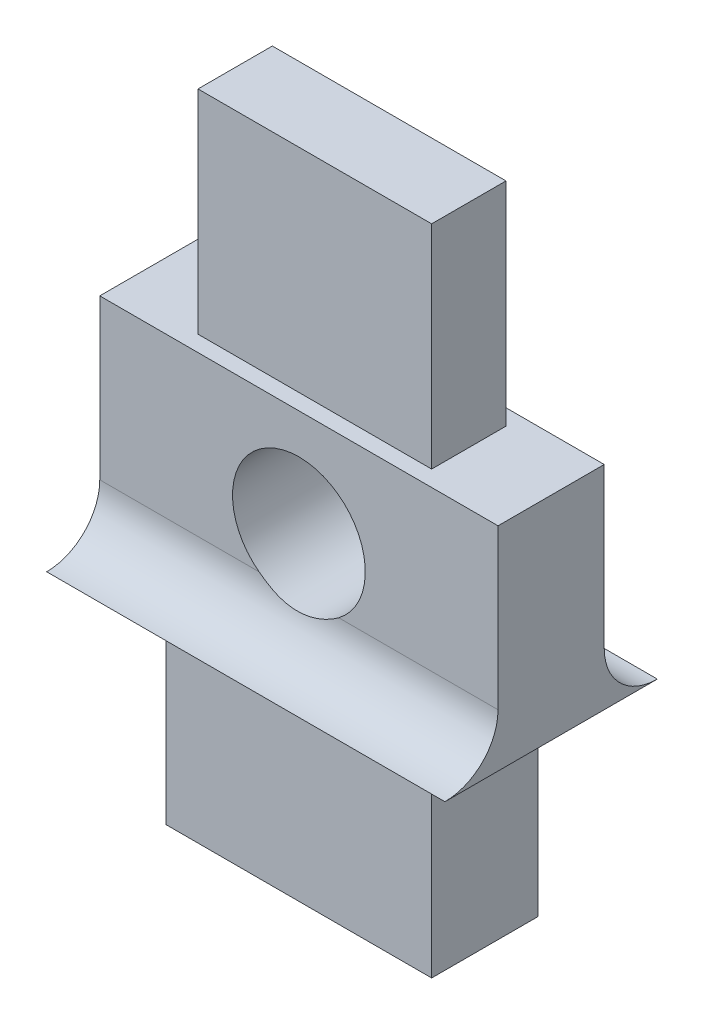
SolidWorks part; units mm, degrees
ref_plane "Front Plane" through (0, 0, 0) normal (0, 0, 1) x (1, 0, 0)
ref_plane "Top Plane" through (0, 0, 0) normal (0, 1, 0) x (1, 0, 0)
ref_plane "Right Plane" through (0, 0, 0) normal (1, 0, 0) x (0, 0, -1)
sketch "Sketch1" plane through (0, 0, 0) normal (0, 0, 1) x (1, 0, 0)
  line L0 (1952.1768, 1466.8841) -> (1957.1768, 1466.8841)
  line L1 (1952.1768, 1454.8841) -> (1957.1768, 1454.8841)
  line L3 (1957.1768, 1458.8841) -> (1957.1768, 1454.8841)
  line L4 (1957.1768, 1458.8841) -> (1958.4268, 1458.8841)
  line L5 (1958.4268, 1462.8841) -> (1958.4268, 1458.8841)
  line L6 (1957.1768, 1462.8841) -> (1957.1768, 1466.8841)
  line L7 (1957.1768, 1462.8841) -> (1958.4268, 1462.8841)
  line L37 (1952.1768, 1458.8841) -> (1950.9268, 1458.8841)
  line L40 (1952.1768, 1458.8841) -> (1952.1768, 1454.8841)
  line L127 (1952.1768, 1462.8841) -> (1950.9268, 1462.8841)
  line L130 (1952.1768, 1462.8841) -> (1952.1768, 1466.8841)
  line L131 (1950.9268, 1462.8841) -> (1950.9268, 1458.8841)
  circle A82 centre (1954.6768, 1460.8841) radius 1.25
  dimension "D1" = 2.5
  dimension "D2" = 1950.9268
  dimension "D3" = 1954.6768
  dimension "D4" = 1957.1768
  dimension "D5" = 1454.8841
  dimension "D6" = 1458.8841
  dimension "D7" = 1460.8841
extrude "Boss-Extrude1" add sketch "Sketch1" along normal blind 2
sketch "Sketch2" plane through (1950.9268, 0, 0) normal (-1, 0, 0) x (0, 0, 1)
  line L0 (1, 1454.8841) -> (1, 1461.8841) construction
  line L1 (2, 1458.8841) -> (2, 1459.8841)
  line L2 (2, 1458.8841) -> (3, 1458.8841)
  line L3 (0, 1458.8841) -> (-1, 1458.8841)
  line L4 (0, 1458.8841) -> (0, 1459.8841)
  arc A0 (2, 1459.8841) -> (3, 1458.8841) centre (3, 1459.8841) ccw
  arc A1 (0, 1459.8841) -> (-1, 1458.8841) centre (-1, 1459.8841) cw
  dimension "D1" = 1
  dimension "D2" = 1
  dimension "D3" = 4
  dimension "D4" = 1
  dimension "D5" = 4
  dimension "D6" = 2
extrude "Boss-Extrude2" add sketch "Sketch2" against normal up to surface (7.5 mm away) up to face at (1958.4268, 1460.8841, 1)
sketch "Sketch3" plane through (0, 0, 2) normal (0, 0, 1) x (1, 0, 0)
  circle A0 centre (1954.6768, 1460.8841) radius 1.25
  dimension "D1" = 2.5
extrude "Cut-Extrude1" cut sketch "Sketch3" against normal through all both and the other way through all
sketch "Sketch4" plane through (0, 1466.8841, 0) normal (0, 1, 0) x (1, 0, 0)
  line L1 (1952.1768, -2) -> (1957.1768, -2)
  line L2 (1952.1768, -2) -> (1952.1768, 0)
  line L3 (1952.1768, 0) -> (1957.1768, 0)
  line L4 (1957.1768, -2) -> (1957.1768, 0)
  line L5 (1952.4768, -1.7) -> (1956.8768, -1.7)
  line L6 (1952.4768, -1.7) -> (1952.4768, -0.3)
  line L7 (1952.4768, -0.3) -> (1956.8768, -0.3)
  line L8 (1956.8768, -1.7) -> (1956.8768, -0.3)
  dimension "D1" = 0.3
  dimension "D2" = 0.3
  dimension "D3" = 0.3
  dimension "D4" = 0.3
extrude "Cut-Extrude2" cut sketch "Sketch4" against normal blind 4
equation "\"D4@Sketch4\"=\"tol2@parametersSketch@prostheticParameters.SLDPRT\""
equation "\"D3@Sketch4\"=\"tol2@parametersSketch@prostheticParameters.SLDPRT\""
equation "\"D2@Sketch4\"=\"tol2@parametersSketch@prostheticParameters.SLDPRT\""
equation "\"D1@Sketch4\"=\"tol2@parametersSketch@prostheticParameters.SLDPRT\""
